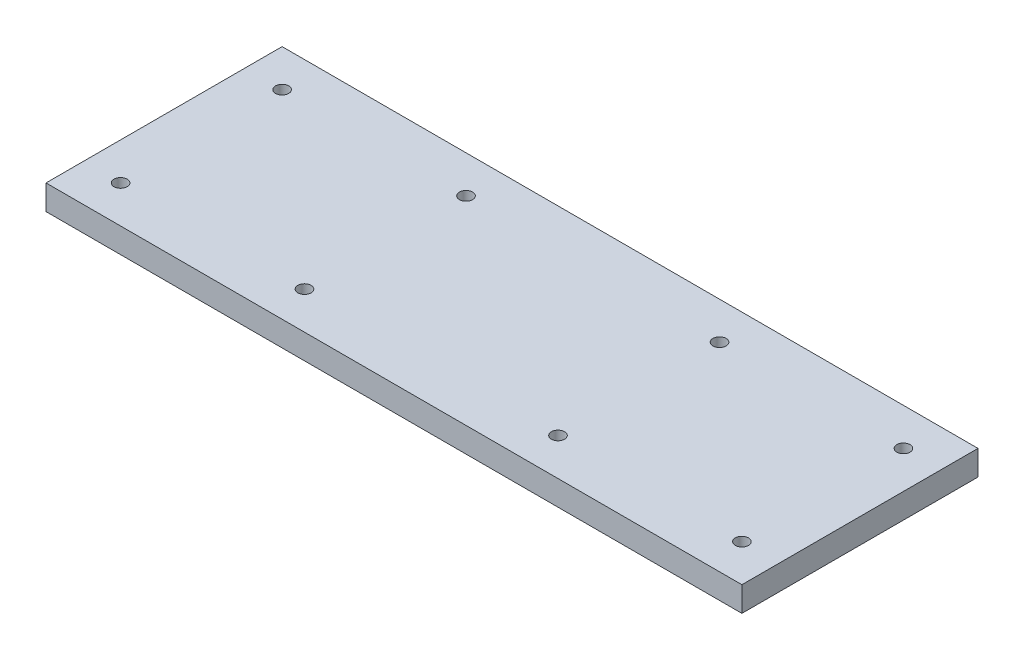
SolidWorks part; units mm, degrees
material "Acrylic (Medium-high impact)"
ref_plane "Front Plane" through (0, 0, 0) normal (0, 0, 1) x (1, 0, 0)
ref_plane "Top Plane" through (0, 0, 0) normal (0, 1, 0) x (1, 0, 0)
ref_plane "Right Plane" through (0, 0, 0) normal (1, 0, 0) x (0, 0, -1)
sketch "Sketch1" plane through (0, 0, 0) normal (0, 1, 0) x (1, 0, 0)
  line L1 (-140, -47.5) -> (140, -47.5)
  line L2 (-140, -47.5) -> (-140, 47.5)
  line L3 (-140, 47.5) -> (140, 47.5)
  line L4 (140, -47.5) -> (140, 47.5)
  line L5 (-140, -47.5) -> (140, 47.5) construction
  line L6 (-140, 47.5) -> (140, -47.5) construction
  point P0 (0, 0)
  dimension "D1" = 280
  dimension "D2" = 95
extrude "Boss-Extrude1" add sketch "Sketch1" along normal blind 10
hole_wizard "M5 Clearance Slot1" positions "Sketch3" profile "Sketch2" size "M5" standard "ANSI Metric" slot yes end condition through all
sketch "Sketch3" plane through (0, 10, 0) normal (0, 1, 0) x (1, 0, 0)
  line L0 (-140, 32.5) -> (140, 32.5) construction
  line L1 (-140, 47.5) -> (-140, -47.5) construction
  line L2 (140, -47.5) -> (140, 47.5) construction
  line L4 (-140, -32.5) -> (140, -32.5) construction
  line L6 (-125, 47.5) -> (-125, -47.5) construction
  line L7 (140, 47.5) -> (-140, 47.5) construction
  line L8 (-140, -47.5) -> (140, -47.5) construction
  line L9 (-36, 47.5) -> (-36, -47.5) construction
  line L12 (51, 47.5) -> (51, -47.5) construction
  line L15 (125, 47.5) -> (125, -47.5) construction
  line L17 (-51, 47.5) -> (-51, -47.5) construction
  line L19 (36, 47.5) -> (36, -47.5) construction
  point P0 (-125, -32.5)
  point P2 (-125, 32.5)
  point P4 (-51, 32.5)
  point P6 (-51, -32.5)
  point P8 (125, 32.5)
  point P10 (125, -32.5)
  point P12 (51, -32.5)
  point P14 (51, 32.5)
  dimension "D1" = 15
  dimension "D2" = 15
  dimension "D3" = 104
  dimension "D4" = 15
  dimension "D5" = 104
  dimension "D6" = 15
  dimension "D7" = 15
  dimension "D8" = 15
sketch "Sketch2" plane through (-125, 10, 32.5) normal (1, 0, 0) x (0, 0, 1)
  line L0 (0, 0) -> (0, 10)
  line L1 (0, 10) -> (2.65, 10)
  line L2 (2.65, 10) -> (2.65, 0)
  line L5 (2.65, 0) -> (0, 0)
  line L11 (0, -6.35) -> (0, 107.95) construction
  dimension "Thru Hole Dia." = 5.3
  dimension "Thru Hole Depth" = 10
